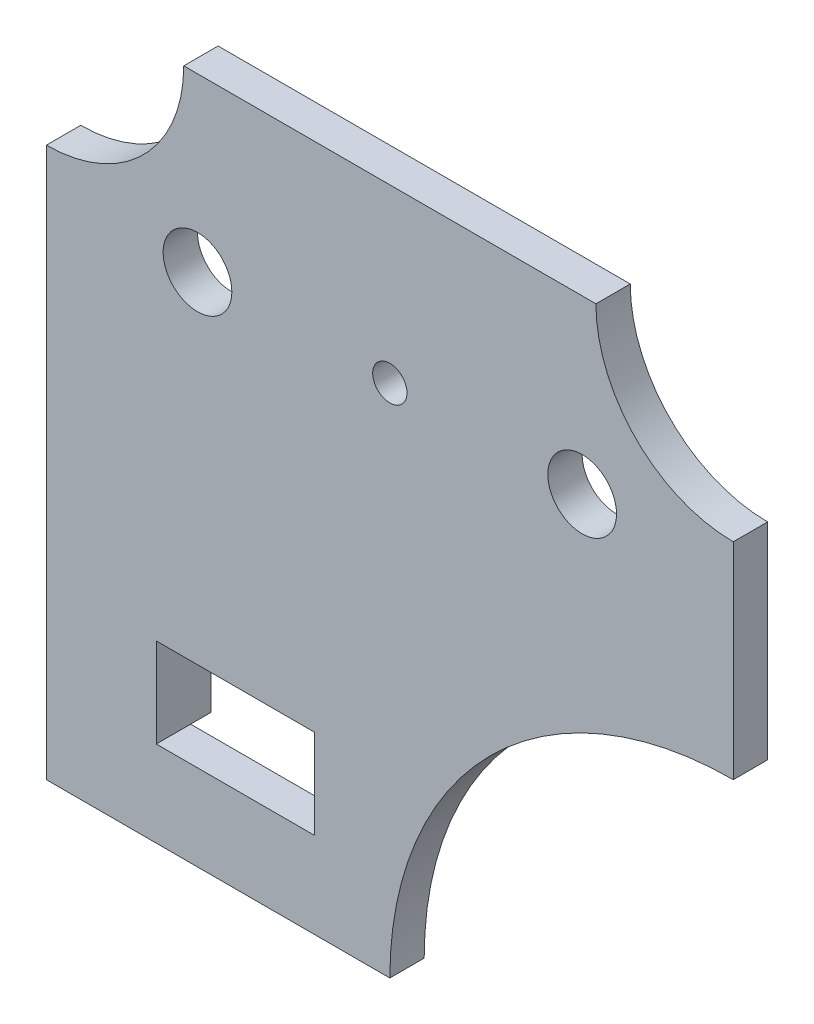
SolidWorks part; units mm, degrees
ref_plane "Alzado" through (0, 0, 0) normal (0, 0, 1) x (1, 0, 0)
ref_plane "Planta" through (0, 0, 0) normal (0, 1, 0) x (1, 0, 0)
ref_plane "Vista lateral" through (0, 0, 0) normal (1, 0, 0) x (0, 0, -1)
sketch "Croquis1" plane through (0, 0, 0) normal (0, 0, 1) x (1, 0, 0)
  line L0 (0, -38.3152) -> (0, 44.837) construction
  line L1 (30, 25) -> (-30, 25)
  line L2 (50, 5) -> (50, -25)
  line L3 (0, -75) -> (-50, -75)
  line L4 (-50, 5) -> (-50, -75)
  line L5 (50, 25) -> (-2.2361, -1.118) construction
  line L6 (2.2361, -1.118) -> (-50, 25) construction
  line L8 (-34, -62.5) -> (-11, -62.5)
  line L9 (-34, -62.5) -> (-34, -49.5)
  line L10 (-34, -49.5) -> (-11, -49.5)
  line L11 (-11, -62.5) -> (-11, -49.5)
  line L12 (-34, -62.5) -> (-11, -49.5) construction
  line L13 (-34, -49.5) -> (-11, -62.5) construction
  circle A0 centre (0, 0) radius 2.5
  circle A1 centre (-28, 0) radius 5
  circle A2 centre (28, 0) radius 5
  circle A3 centre (-28, -56) radius 2.35 construction
  arc A4 (50, -25) -> (0, -75) centre (50, -75) ccw
  arc A5 (-50, 5) -> (-30, 25) centre (-50, 25) ccw
  arc A6 (30, 25) -> (50, 5) centre (50, 25) ccw
  point P0 (0, 0)
  point P21 (-22.5, -56)
  dimension "D3" = 5
  dimension "D4" = 10
  dimension "D6" = 4.7
  dimension "D7" = 56
  dimension "D14" = 100
  dimension "D15" = 40
  dimension "D1" = 100
  dimension "D2" = 75
  dimension "D5" = 28
  dimension "D8" = 25
  dimension "D9" = 50
  dimension "D10" = 23
  dimension "D11" = 13
  dimension "D12" = 6.5
  dimension "D13" = 6
extrude "Saliente-Extruir1" add sketch "Croquis1" along normal mid plane 5
sketch "Croquis2" plane through (0, 0, 2.5) normal (0, 0, 1) x (1, 0, 0)
  line L0 (-11, -49.5) -> (-34, -49.5) construction
  line L1 (-6.5, -49.5) -> (-38.5, -49.5)
  line L2 (-6.5, -49.5) -> (-6.5, -62.5)
  line L3 (-6.5, -62.5) -> (-38.5, -62.5)
  line L4 (-38.5, -49.5) -> (-38.5, -62.5)
  line L7 (-34, -49.5) -> (-34, -62.5) construction
  line L9 (-11, -49.5) -> (-34, -49.5)
  line L10 (-11, -49.5) -> (-11, -62.5)
  line L11 (-11, -62.5) -> (-34, -62.5)
  line L12 (-34, -49.5) -> (-34, -62.5)
  point P0 (-22.5, -56)
  point P8 (-22.5, -49.5)
  point P11 (-34, -56)
  point P12 (-38.5, -56)
  point P13 (-22.5, -56)
  line M23 (-11, -49.5) -> (-11, -62.5)
  line M25 (-34, -62.5) -> (-34, -49.5)
  dimension "D1" = 13
  dimension "D2" = 32
extrude "Saliente-Extruir2" add sketch "Croquis2" against normal blind 8 contours L1 L4 L3 M25 | L3 L2 L1 M23
